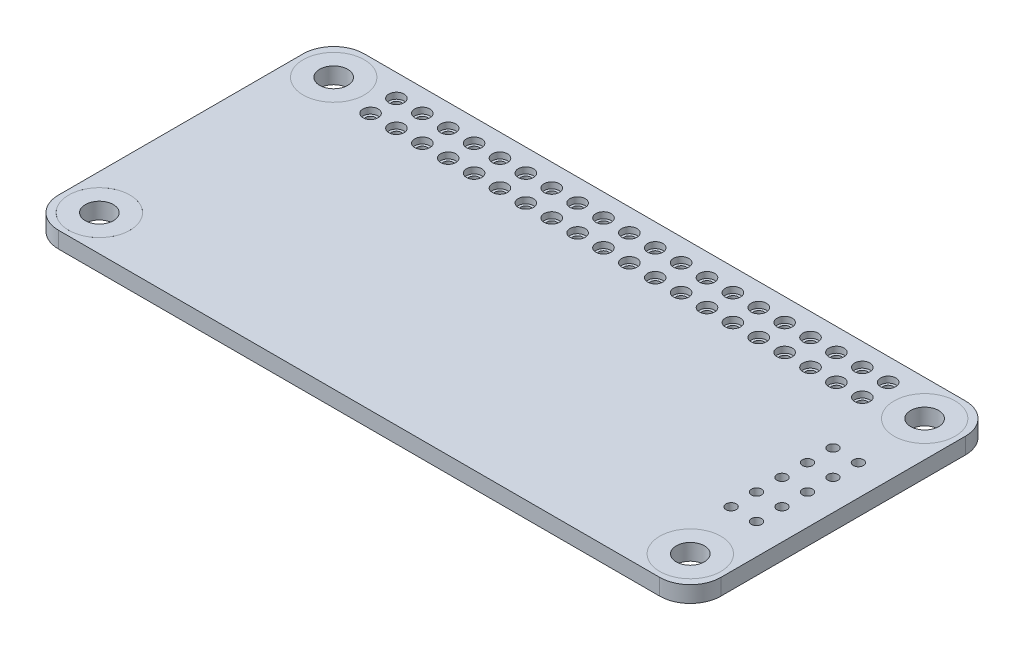
SolidWorks part; units mm, degrees
ref_plane "Front Plane" through (0, 0, 0) normal (0, 0, 1) x (1, 0, 0)
ref_plane "Top Plane" through (0, 0, 0) normal (0, 1, 0) x (1, 0, 0)
ref_plane "Right Plane" through (0, 0, 0) normal (1, 0, 0) x (0, 0, -1)
sketch "Sketch1" plane through (0, 0, 0) normal (0, 1, 0) x (1, 0, 0)
  line L0 (-27.4768, 39.9178) -> (-27.4768, -37.6558) construction
  line L1 (-29.5, -15) -> (29.5, -15)
  line L2 (-32.5, -12) -> (-32.5, 12)
  line L3 (-29.5, 15) -> (29.5, 15)
  line L4 (32.5, -12) -> (32.5, 12)
  line L5 (-32.5, -15) -> (32.5, 15) construction
  line L6 (-32.5, 15) -> (32.5, -15) construction
  line L7 (0, 0) -> (0, 39.9178) construction
  line L9 (-25.5, 14.1112) -> (25.5, 14.1112) construction
  line L10 (-25.5, 14.1112) -> (-25.5, 8.9112) construction
  line L11 (-25.5, 8.9112) -> (25.5, 8.9112) construction
  line L12 (25.5, 14.1112) -> (25.5, 8.9112) construction
  arc A0 (-32.5, 12) -> (-29.5, 15) centre (-29.5, 12) cw
  arc A1 (-29.5, -15) -> (-32.5, -12) centre (-29.5, -12) cw
  arc A2 (29.5, -15) -> (32.5, -12) centre (29.5, -12) ccw
  arc A3 (29.5, 15) -> (32.5, 12) centre (29.5, 12) cw
  circle A4 centre (-29, 11.5) radius 3
  circle A5 centre (-29, -11.5) radius 3
  circle A6 centre (29, -11.5) radius 3
  circle A7 centre (-24.13, 12.7877) radius 0.75
  circle A8 centre (-21.59, 12.7877) radius 0.75
  circle A9 centre (-19.05, 12.7877) radius 0.75
  circle A10 centre (-16.51, 12.7877) radius 0.75
  circle A11 centre (-13.97, 12.7877) radius 0.75
  circle A12 centre (-11.43, 12.7877) radius 0.75
  circle A13 centre (-8.89, 12.7877) radius 0.75
  circle A14 centre (-6.35, 12.7877) radius 0.75
  circle A15 centre (-3.81, 12.7877) radius 0.75
  circle A16 centre (-1.27, 12.7877) radius 0.75
  circle A17 centre (1.27, 12.7877) radius 0.75
  circle A18 centre (3.81, 12.7877) radius 0.75
  circle A19 centre (6.35, 12.7877) radius 0.75
  circle A20 centre (8.89, 12.7877) radius 0.75
  circle A21 centre (11.43, 12.7877) radius 0.75
  circle A22 centre (13.97, 12.7877) radius 0.75
  circle A23 centre (16.51, 12.7877) radius 0.75
  circle A24 centre (19.05, 12.7877) radius 0.75
  circle A25 centre (21.59, 12.7877) radius 0.75
  circle A26 centre (24.13, 12.7877) radius 0.75
  circle A27 centre (-21.59, 10.2477) radius 0.75
  circle A28 centre (-19.05, 10.2477) radius 0.75
  circle A29 centre (-16.51, 10.2477) radius 0.75
  circle A30 centre (-13.97, 10.2477) radius 0.75
  circle A31 centre (-11.43, 10.2477) radius 0.75
  circle A32 centre (-8.89, 10.2477) radius 0.75
  circle A33 centre (-6.35, 10.2477) radius 0.75
  circle A34 centre (-3.81, 10.2477) radius 0.75
  circle A35 centre (-1.27, 10.2477) radius 0.75
  circle A36 centre (1.27, 10.2477) radius 0.75
  circle A37 centre (3.81, 10.2477) radius 0.75
  circle A38 centre (6.35, 10.2477) radius 0.75
  circle A39 centre (8.89, 10.2477) radius 0.75
  circle A40 centre (11.43, 10.2477) radius 0.75
  circle A41 centre (13.97, 10.2477) radius 0.75
  circle A42 centre (16.51, 10.2477) radius 0.75
  circle A43 centre (19.05, 10.2477) radius 0.75
  circle A44 centre (21.59, 10.2477) radius 0.75
  circle A45 centre (24.13, 10.2477) radius 0.75
  circle A46 centre (-24.13, 10.2477) radius 0.75
  circle A49 centre (29, 11.5) radius 3
  point P0 (0, 0)
  point P32 (0, 8.9112)
  dimension "D3" = 3
  dimension "D4" = 51
  dimension "D5" = 6
  dimension "D11" = 1.5
  dimension "D12" = 2
  dimension "D27" = 6
  dimension "D28" = 6
  dimension "D1" = 65
  dimension "D2" = 30
  dimension "D6" = 23
  dimension "D7" = 29
  dimension "D8" = 3.5
  dimension "D9" = 5.2
  dimension "D10" = 29
  dimension "D13" = 1.27
  dimension "D14" = 20
extrude "Boss-Extrude1" add sketch "Sketch1" along normal blind 1.6
sketch "Sketch2" plane through (0, 0, 0) normal (0, 1, 0) x (1, 0, 0)
  circle A0 centre (-24.13, 12.7877) radius 0.75 construction
  circle A1 centre (-24.13, 12.7877) radius 0.75
  circle A3 centre (-24.13, 12.7877) radius 0.5
  dimension "D1" = 1
extrude "Boss-Extrude2" add sketch "Sketch2" along normal blind 1 separate body
pattern_linear "LPattern2" count 20 spacing 2.54 along (1, 0, 0) count 2 spacing 2.54 along (0, 0, 1) of bodies 102
sketch "Sketch4" plane through (0, 0, 0) normal (0, 1, 0) x (1, 0, 0)
  circle A0 centre (-29, 11.5) radius 3
  circle A1 centre (-29, 11.5) radius 1.375
  dimension "D1" = 2.75
extrude "Boss-Extrude4" add sketch "Sketch4" along normal blind 1.6 separate body
mirror "Mirror1" about plane through (0, 0, 0) normal (1, 0, 0) of bodies 147
mirror "Mirror2" about plane through (0, 0, 0) normal (0, 0, 1) of bodies 147 148
sketch "Esquisse1" plane through (0, 0, 0) normal (0, 1, 0) x (1, 0, 0)
  line L0 (32.5, -12) -> (32.5, 12) construction
  line L1 (29.5, 15) -> (-29.5, 15) construction
  circle A0 centre (29.5, 4.5) radius 0.5
  dimension "D1" = 1
  dimension "D2" = 3
  dimension "D3" = 10.5
extrude "Enlèv. mat.-Extru.3" cut sketch "Esquisse1" against normal through all and the other way through all
pattern_linear "Répétition linéaire1" count 5 spacing 2.5 along (0, 0, 1) count 2 spacing 2.5 along (-1, 0, 0) of "Enlèv. mat.-Extru.3"
equation "\"2.5.00mm\"=10"
